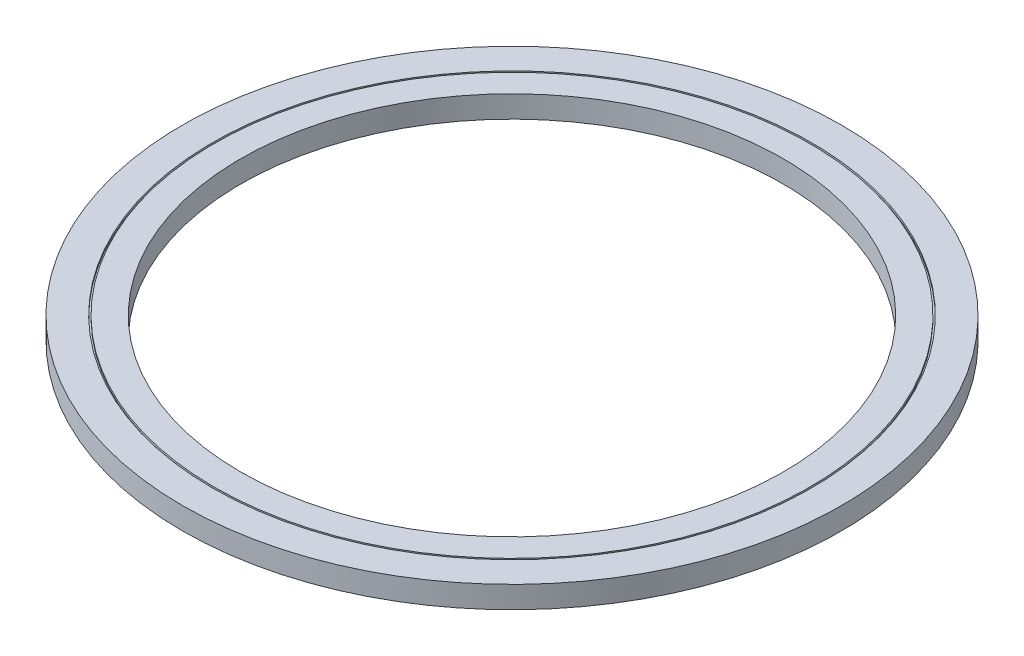
SolidWorks part; units mm, degrees
ref_plane "Front Plane" through (0, 0, 0) normal (0, 0, 1) x (1, 0, 0)
ref_plane "Top Plane" through (0, 0, 0) normal (0, 1, 0) x (1, 0, 0)
ref_plane "Right Plane" through (0, 0, 0) normal (1, 0, 0) x (0, 0, -1)
sketch "Sketch1" plane through (0, 0, 0) normal (0, 1, 0) x (1, 0, 0)
  circle A0 centre (0, 0) radius 150
  circle A1 centre (0, 0) radius 123.5
  dimension "D1" = 247
  dimension "D2" = 300
extrude "Boss-Extrude1" add sketch "Sketch1" along normal mid plane 10
sketch "Sketch2" plane through (0, 5, 0) normal (0, 1, 0) x (1, 0, 0)
  circle A0 centre (0, 0) radius 135.5
  circle A1 centre (0, 0) radius 136.25
  dimension "D1" = 271
  dimension "D2" = 272.5
extrude "Cut-Extrude1" cut sketch "Sketch2" against normal blind 1
mirror "Mirror1" about plane through (0, 0, 0) normal (0, 1, 0) of "Cut-Extrude1"
